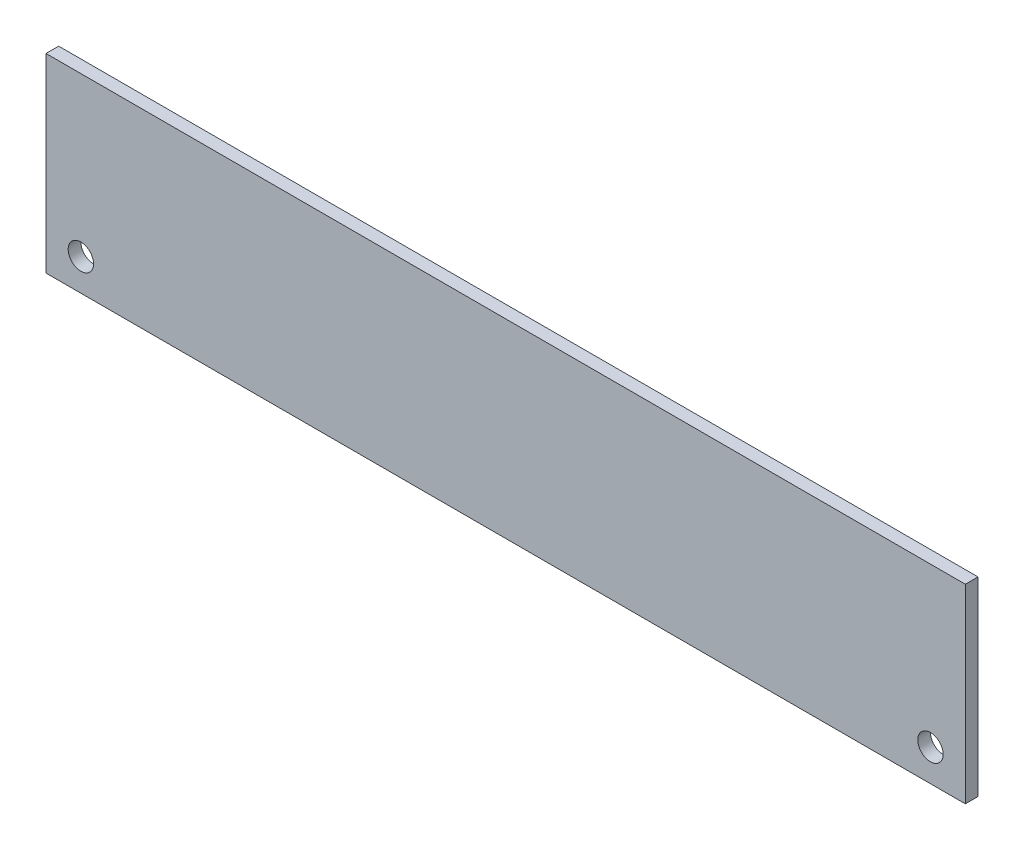
SolidWorks part; units mm, degrees
ref_plane "Plan de face" through (0, 0, 0) normal (0, 0, 1) x (1, 0, 0)
ref_plane "Plan de dessus" through (0, 0, 0) normal (0, 1, 0) x (1, 0, 0)
ref_plane "Plan de droite" through (0, 0, 0) normal (1, 0, 0) x (0, 0, -1)
sketch "Esquisse1" plane through (0, 0, 0) normal (0, 0, 1) x (1, 0, 0)
  line L0 (-72.5, 0) -> (-72.5, 5) construction
  line L1 (0, 0) -> (-145, 0)
  line L2 (0, 0) -> (0, 30)
  line L3 (0, 30) -> (-145, 30)
  line L4 (-145, 0) -> (-145, 30)
  line L5 (-72.5, 5) -> (-5.5, 5) construction
  line L6 (-72.5, 5) -> (-139.5, 5) construction
  circle A0 centre (-5.5, 5) radius 2
  circle A1 centre (-139.5, 5) radius 2
  dimension "D3" = 4
  dimension "D1" = 134
  dimension "D2" = 5
  dimension "D4" = 30
  dimension "D5" = 145
extrude "Extrusion1" add sketch "Esquisse1" along normal blind 2
